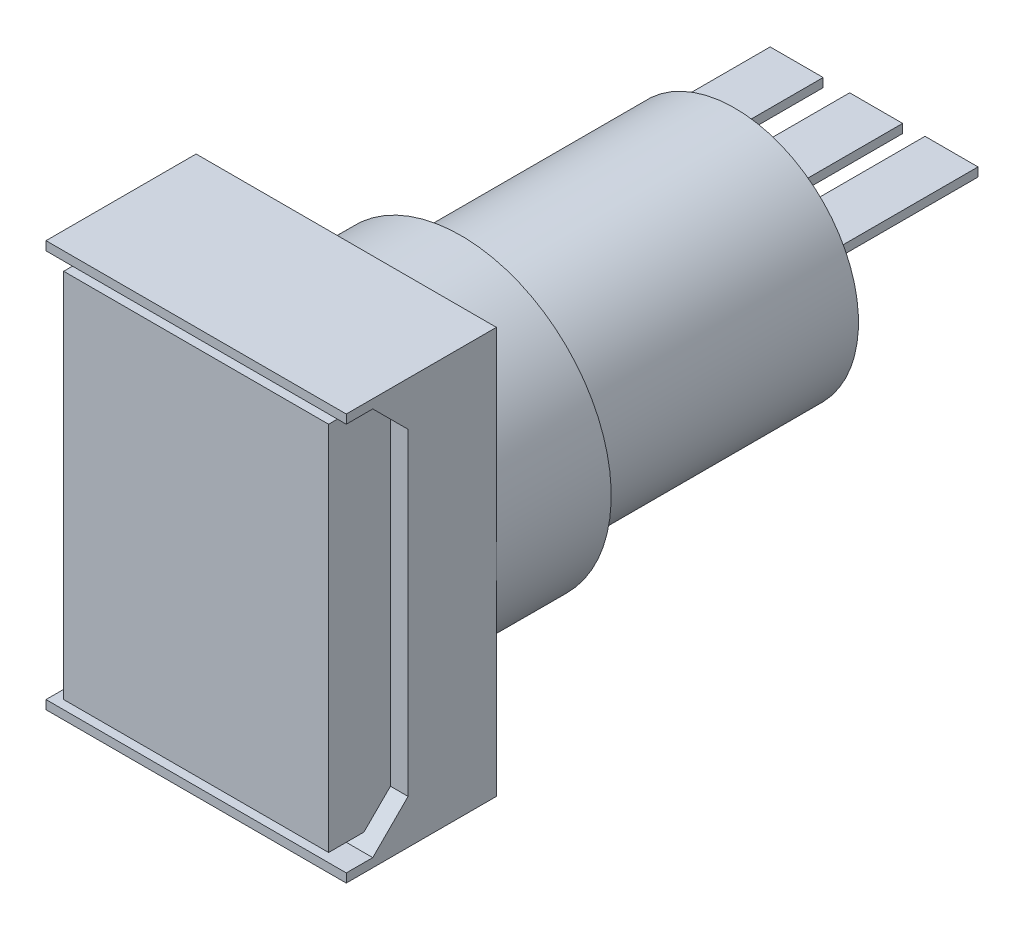
SolidWorks part; units mm, degrees
material "ABS"
ref_plane "正面" through (0, 0, 0) normal (0, 0, 1) x (1, 0, 0)
ref_plane "平面" through (0, 0, 0) normal (0, 1, 0) x (1, 0, 0)
ref_plane "右側面" through (0, 0, 0) normal (1, 0, 0) x (0, 0, -1)
ref_plane "平面1" through (0, 0, 0) normal (0, 0, 1) x (1, 0, 0)
sketch "ｽｹｯﾁ1" plane through (0, 0, 0) normal (0, 0, 1) x (1, 0, 0)
  line L1 (8.5, 11.5) -> (-8.5, 11.5)
  line L2 (8.5, 11.5) -> (8.5, -11.5)
  line L3 (8.5, -11.5) -> (-8.5, -11.5)
  line L4 (-8.5, 11.5) -> (-8.5, -11.5)
  line L5 (8.5, 11.5) -> (-8.5, -11.5) construction
  line L6 (8.5, -11.5) -> (-8.5, 11.5) construction
  point P0 (0, 0)
  dimension "D1" = 23
  dimension "D2" = 17
extrude "ﾎﾞｽ - 押し出し1" add sketch "ｽｹｯﾁ1" along normal blind 8.5
sketch "ｽｹｯﾁ2" plane through (8.5, 0, 0) normal (1, 0, 0) x (0, 0, -1)
  line L0 (-8.5, 11) -> (-7, 11)
  line L1 (-8.5, -11.5) -> (-8.5, 11.5) construction
  line L2 (-7, 11) -> (-5, 9)
  line L3 (-5, 9) -> (-5, -9)
  line L4 (-5, -9) -> (-7, -11)
  line L5 (-7, -11) -> (-8.5, -11)
  line L6 (-8.5, -11) -> (-8.5, 11)
  line L7 (0, 55) -> (0, -55) construction
  line L8 (-8.5, 11.5) -> (0, 11.5) construction
  point P12 (-5, 0)
  dimension "D1" = 5
  dimension "D2" = 1.5
  dimension "D3" = 1.5
  dimension "D4" = 0.5
extrude "ｶｯﾄ - 押し出し1" cut sketch "ｽｹｯﾁ2" against normal blind 20
sketch "ｽｹｯﾁ3" plane through (0, 0, 5) normal (0, 0, 1) x (1, 0, 0)
  line L1 (7.5, 10.5) -> (-7.5, 10.5)
  line L2 (7.5, 10.5) -> (7.5, -10.5)
  line L3 (7.5, -10.5) -> (-7.5, -10.5)
  line L4 (-7.5, 10.5) -> (-7.5, -10.5)
  line L5 (7.5, 10.5) -> (-7.5, -10.5) construction
  line L6 (7.5, -10.5) -> (-7.5, 10.5) construction
  point P0 (0, 0)
  dimension "D1" = 21
  dimension "D2" = 15
extrude "ﾎﾞｽ - 押し出し2" add sketch "ｽｹｯﾁ3" along normal blind 3.5
sketch "ｽｹｯﾁ4" plane through (0, 0, 0) normal (0, 0, -1) x (-1, 0, 0)
  circle A0 centre (0, 0) radius 8.5
  dimension "D1" = 17
extrude "ﾎﾞｽ - 押し出し3" add sketch "ｽｹｯﾁ4" along normal blind 6.5
sketch "ｽｹｯﾁ5" plane through (0, 0, 0) normal (0, 0, -1) x (-1, 0, 0)
  circle A0 centre (0, 0) radius 7
  dimension "D1" = 14
extrude "ﾎﾞｽ - 押し出し4" add sketch "ｽｹｯﾁ5" along normal blind 22
sketch "ｽｹｯﾁ6" plane through (0, 0, -22) normal (0, 0, -1) x (-1, 0, 0)
  line L5 (-5.7663, 3) -> (-2.7663, 3)
  line L6 (-5.7663, 3) -> (-5.7663, 2.5)
  line L11 (-5.7663, 2.5) -> (-2.7663, 2.5)
  line L12 (-2.7663, 3) -> (-2.7663, 2.5)
  line L17 (-5.7663, 3) -> (-2.7663, 2.5) construction
  line L18 (-5.7663, 2.5) -> (-2.7663, 3) construction
  line L19 (-1.5, 3) -> (1.5, 3)
  line L20 (-1.5, 3) -> (-1.5, 2.5)
  line L21 (-1.5, 2.5) -> (1.5, 2.5)
  line L22 (1.5, 3) -> (1.5, 2.5)
  line L23 (-1.5, 3) -> (1.5, 2.5) construction
  line L24 (-1.5, 2.5) -> (1.5, 3) construction
  line L25 (3, 3) -> (6, 3)
  line L26 (3, 3) -> (3, 2.5)
  line L27 (3, 2.5) -> (6, 2.5)
  line L28 (6, 3) -> (6, 2.5)
  line L29 (3, 3) -> (6, 2.5) construction
  line L30 (3, 2.5) -> (6, 3) construction
  point P0 (-4.2663, 2.75)
  point P5 (0, 2.75)
  point P10 (4.5, 2.75)
  dimension "D1" = 0.5
  dimension "D2" = 3
  dimension "D3" = 0.5
  dimension "D4" = 3
  dimension "D5" = 0.5
  dimension "D6" = 3
  dimension "D7" = 6.5
  dimension "D8" = 6.5
  dimension "D9" = 2.5
extrude "ﾎﾞｽ - 押し出し5" add sketch "ｽｹｯﾁ6" along normal blind 8
sketch "ｽｹｯﾁ7" plane through (0, 0, -22) normal (0, 0, -1) x (-1, 0, 0)
  circle A0 centre (0, 0) radius 6.5
  dimension "D1" = 13
extrude "ﾎﾞｽ - 押し出し6" add sketch "ｽｹｯﾁ7" along normal blind 0.01
